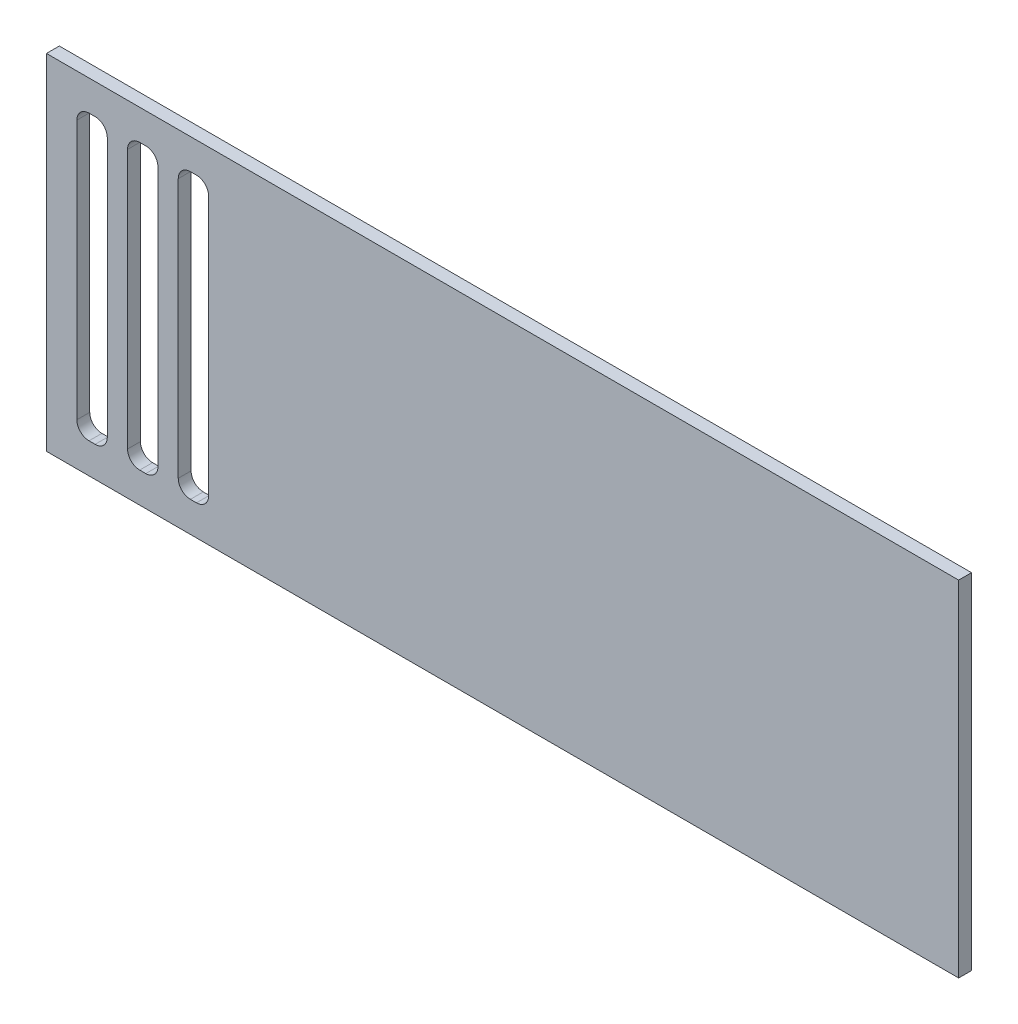
SolidWorks part; units mm, degrees
ref_plane "Front Plane" through (0, 0, 0) normal (0, 0, 1) x (1, 0, 0)
ref_plane "Top Plane" through (0, 0, 0) normal (0, 1, 0) x (1, 0, 0)
ref_plane "Right Plane" through (0, 0, 0) normal (1, 0, 0) x (0, 0, -1)
sketch "Sketch1" plane through (0, 0, 0) normal (0, 0, 1) x (1, 0, 0)
  line L1 (0, 0) -> (450, 0)
  line L2 (0, 0) -> (0, 170)
  line L3 (0, 170) -> (450, 170)
  line L4 (450, 0) -> (450, 170)
extrude "Boss-Extrude1" add sketch "Sketch1" along normal blind 6.35
sketch "Sketch2" plane through (0, 0, 6.35) normal (0, 0, 1) x (1, 0, 0)
  line L6 (15, 15) -> (15, 155)
  line L7 (15, 155) -> (30, 155)
  line L8 (30, 155) -> (30, 15)
  line L9 (30, 15) -> (15, 15)
  line L11 (40, 15) -> (40, 155)
  line L12 (40, 155) -> (55, 155)
  line L13 (55, 155) -> (55, 15)
  line L14 (55, 15) -> (40, 15)
  line L16 (65, 15) -> (80, 15)
  line L17 (80, 15) -> (80, 155)
  line L18 (80, 155) -> (65, 155)
  line L19 (65, 155) -> (65, 15)
extrude "Cut-Extrude1" cut sketch "Sketch2" against normal through all both and the other way through all
fillet "Fillet1" radius 6 6 edges at (15, 155, 3.175) (40, 155, 3.175) (65, 155, 3.175) (30, 155, 3.175) (55, 155, 3.175) (80, 155, 3.175)
fillet "Fillet2" radius 6 6 edges at (30, 15, 3.175) (55, 15, 3.175) (80, 15, 3.175) (65, 15, 3.175) (40, 15, 3.175) (15, 15, 3.175)
